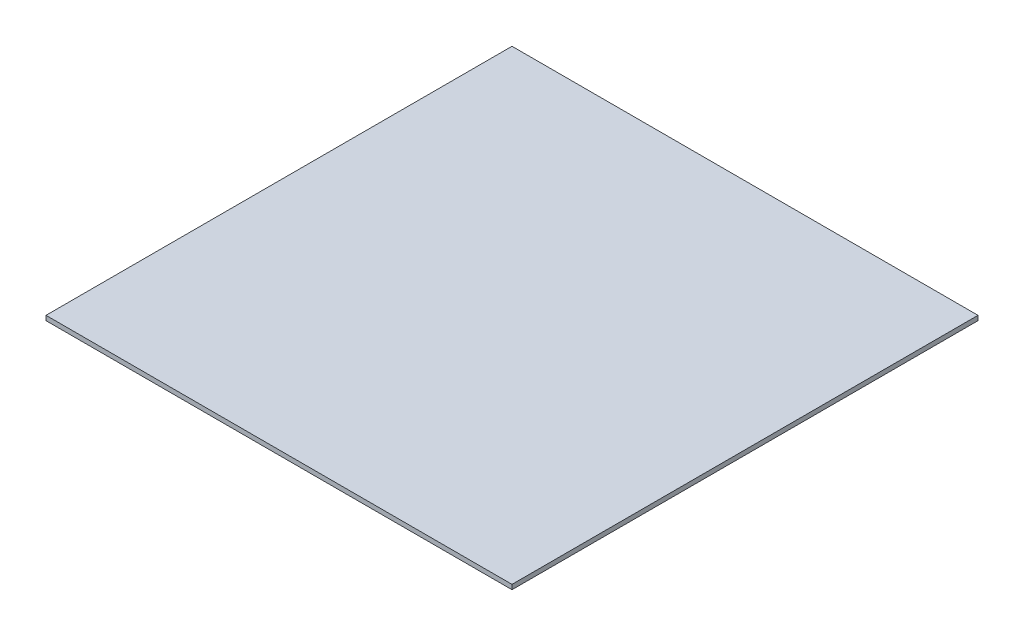
SolidWorks part; units mm, degrees
ref_plane "Front Plane" through (0, 0, 0) normal (0, 0, 1) x (1, 0, 0)
ref_plane "Top Plane" through (0, 0, 0) normal (0, 1, 0) x (1, 0, 0)
ref_plane "Right Plane" through (0, 0, 0) normal (1, 0, 0) x (0, 0, -1)
sketch "Sketch1" plane through (0, 0, 0) normal (0, 1, 0) x (1, 0, 0)
  line L1 (5000, -5000) -> (-5000, -5000)
  line L2 (5000, -5000) -> (5000, 5000)
  line L3 (5000, 5000) -> (-5000, 5000)
  line L4 (-5000, -5000) -> (-5000, 5000)
  line L5 (5000, -5000) -> (-5000, 5000) construction
  line L6 (5000, 5000) -> (-5000, -5000) construction
  point P0 (0, 0)
  dimension "D1" = 10000
  dimension "D2" = 10000
extrude "Boss-Extrude1" add sketch "Sketch1" along normal blind 100
